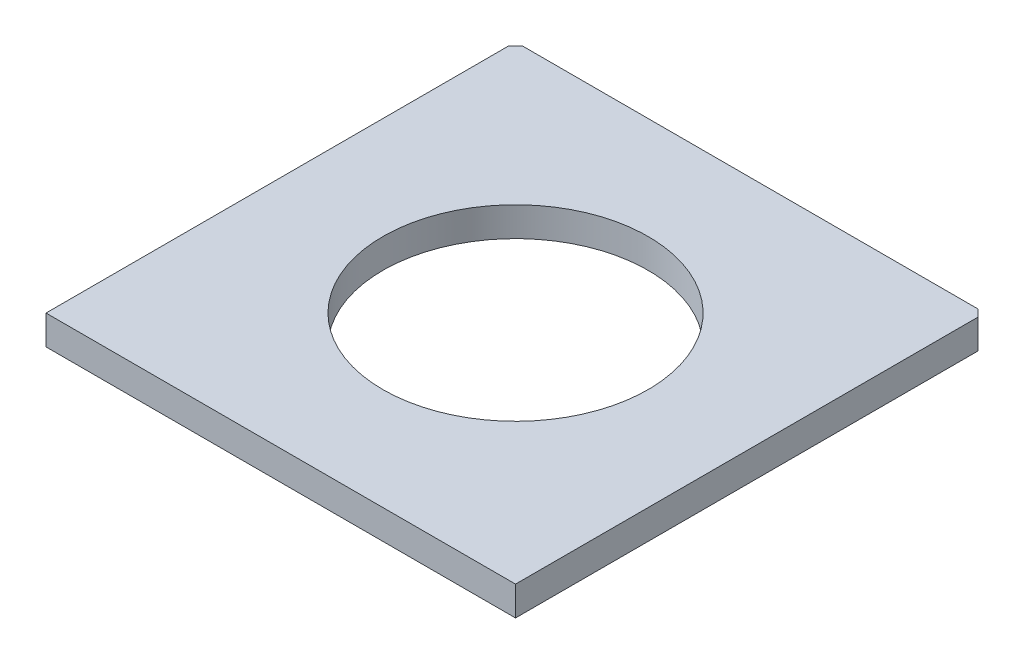
SolidWorks part; units mm, degrees
ref_plane "Front Plane" through (0, 0, 0) normal (0, 0, 1) x (1, 0, 0)
ref_plane "Top Plane" through (0, 0, 0) normal (0, 1, 0) x (1, 0, 0)
ref_plane "Right Plane" through (0, 0, 0) normal (1, 0, 0) x (0, 0, -1)
sketch "Sketch1" plane through (0, 0, 0) normal (0, 1, 0) x (1, 0, 0)
  line L1 (-25.4, -25.4) -> (25.4, -25.4)
  line L2 (-25.4, -25.4) -> (-25.4, 25.4)
  line L3 (-25.4, 25.4) -> (25.4, 25.4)
  line L4 (25.4, -25.4) -> (25.4, 25.4)
  line L5 (-25.4, -25.4) -> (25.4, 25.4) construction
  line L6 (-25.4, 25.4) -> (25.4, -25.4) construction
  point P0 (0, 0)
extrude "Boss-Extrude1" add sketch "Sketch1" along normal blind 3.175
sketch "Sketch2" plane through (0, 3.175, 0) normal (0, 1, 0) x (1, 0, 0)
  circle A0 centre (0, 0) radius 14.35
extrude "Cut-Extrude1" cut sketch "Sketch2" against normal blind 3.175
sketch "Sketch3" plane through (0, 3.175, 0) normal (0, 1, 0) x (1, 0, 0)
  line L0 (-25.4, 25.4) -> (-24.638, 25.4)
  line L1 (25.4, 25.4) -> (-25.4, 25.4) construction
  line L2 (-24.638, 25.4) -> (-25.4, 24.638)
  line L3 (-25.4, 25.4) -> (-25.4, -25.4) construction
  line L4 (-25.4, 24.638) -> (-25.4, 25.4)
  line L11 (25.4, -25.4) -> (25.4, 25.4) construction
  line L13 (25.4, 25.4) -> (25.4, 24.638)
  line L14 (25.4, 24.638) -> (24.638, 25.4)
  line L15 (24.638, 25.4) -> (25.4, 25.4)
extrude "Cut-Extrude2" cut sketch "Sketch3" against normal blind 3.175
